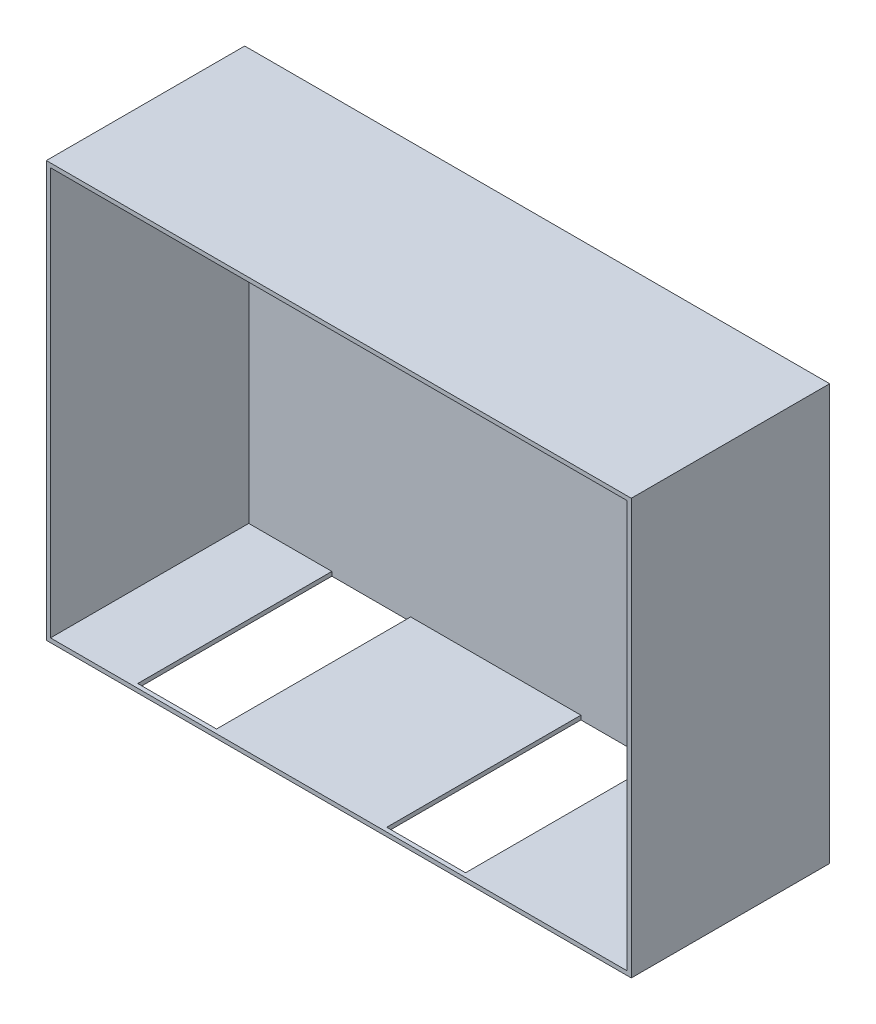
SolidWorks part; units mm, degrees
ref_plane "Alzado" through (0, 0, 0) normal (0, 0, 1) x (1, 0, 0)
ref_plane "Planta" through (0, 0, 0) normal (0, 1, 0) x (1, 0, 0)
ref_plane "Vista lateral" through (0, 0, 0) normal (1, 0, 0) x (0, 0, -1)
sketch "Croquis1" plane through (0, 0, 0) normal (0, 0, 1) x (1, 0, 0)
  line L0 (-3540, 2514.5) -> (-3540, -2514.5)
  line L1 (-3490, 2464.5) -> (3490, 2464.5)
  line L2 (-3490, 2464.5) -> (-3490, -2464.5)
  line L3 (-3490, -2464.5) -> (3490, -2464.5)
  line L4 (3490, 2464.5) -> (3490, -2464.5)
  line L5 (-3490, 2464.5) -> (3490, -2464.5) construction
  line L6 (-3490, -2464.5) -> (3490, 2464.5) construction
  line L7 (-3540, -2514.5) -> (3540, -2514.5)
  line L8 (3540, 2514.5) -> (3540, -2514.5)
  line L9 (-3540, 2514.5) -> (3540, 2514.5)
  point P0 (0, 0)
  dimension "D1" = 6980
  dimension "D2" = 4929
  dimension "D3" = 50
extrude "Saliente-Extruir1" add sketch "Croquis1" along normal blind 2400
sketch "Croquis2" plane through (0, -2514.5, 0) normal (0, -1, 0) x (1, 0, 0)
  line L0 (-3540, 0) -> (3540, 0) construction
  line L1 (-2484, 2350) -> (-1530, 2350)
  line L2 (-2484, 2350) -> (-2484, 0)
  line L3 (-2484, 0) -> (-1530, 0)
  line L4 (-1530, 2350) -> (-1530, 0)
  line L5 (-2484, 2350) -> (-1530, 0) construction
  line L6 (-2484, 0) -> (-1530, 2350) construction
  line L7 (-3540, 2400) -> (3540, 2400) construction
  line L8 (-3540, 2400) -> (-3540, 0) construction
  line L10 (530, 2350) -> (1484, 2350)
  line L11 (530, 2350) -> (530, 0)
  line L12 (530, 0) -> (1484, 0)
  line L13 (1484, 2350) -> (1484, 0)
  line L14 (530, 2350) -> (1484, 0) construction
  line L15 (530, 0) -> (1484, 2350) construction
  point P0 (-2007, 1175)
  point P11 (1007, 1175)
  dimension "D1" = 0
  dimension "D2" = 954
  dimension "D3" = 50
  dimension "D4" = 1056
  dimension "D5" = 50
  dimension "D6" = 0
  dimension "D7" = 2060
  dimension "D8" = 954
extrude "Cortar-Extruir1" cut sketch "Croquis2" against normal up to next
sketch "Croquis3" plane through (0, 0, 0) normal (0, 0, -1) x (-1, 0, 0)
  line L1 (-3540, 2514.5) -> (3540, 2514.5)
  line L2 (-3540, 2514.5) -> (-3540, -2514.5)
  line L3 (-3540, -2514.5) -> (3540, -2514.5)
  line L4 (3540, 2514.5) -> (3540, -2514.5)
extrude "Saliente-Extruir2" add sketch "Croquis3" along normal blind 1
sketch "Croquis4" plane through (0, 0, 0) normal (0, 0, 1) x (1, 0, 0)
  line L0 (-3490, 2464.5) -> (-3490, -2464.5) construction
  line L1 (3490, 2464.5) -> (-3490, 2464.5) construction
  circle A0 centre (-1986, 489.5) radius 10
  dimension "D1" = 20
  dimension "D2" = 1504
  dimension "D3" = 1975
extrude "Cortar-Extruir2" cut sketch "Croquis4" against normal up to next
